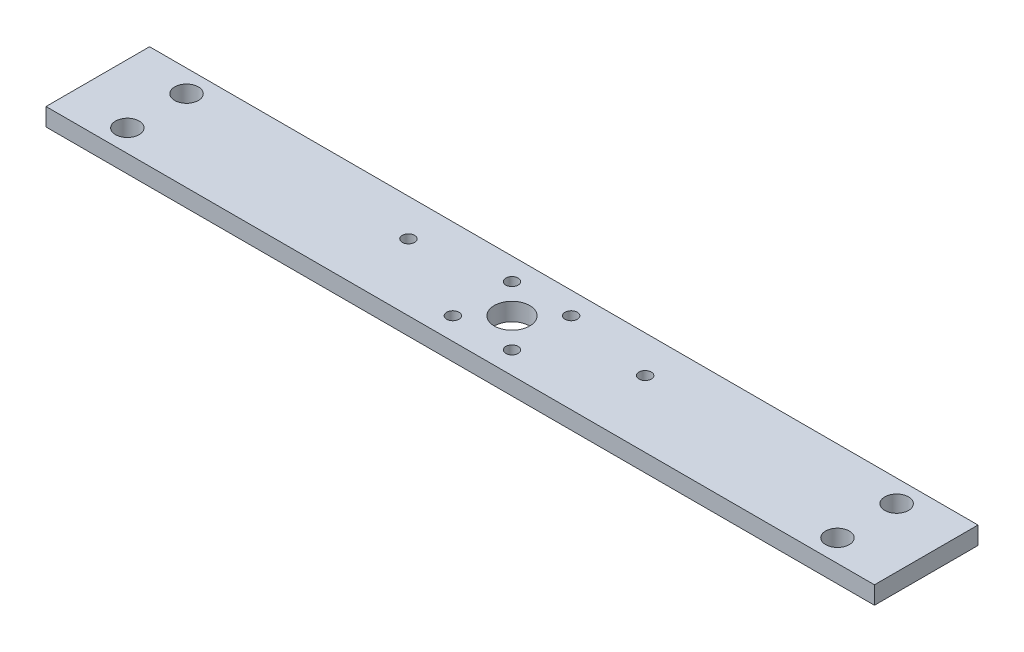
SolidWorks part; units mm, degrees
ref_plane "Front Plane" through (0, 0, 0) normal (0, 0, 1) x (1, 0, 0)
ref_plane "Top Plane" through (0, 0, 0) normal (0, 1, 0) x (1, 0, 0)
ref_plane "Right Plane" through (0, 0, 0) normal (1, 0, 0) x (0, 0, -1)
sketch "Sketch1" plane through (0, 0, 0) normal (0, 1, 0) x (1, 0, 0)
  line L0 (0, -55) -> (0, 55) construction
  line L1 (-140, 17.5) -> (140, 17.5)
  line L2 (-140, 17.5) -> (-140, -17.5)
  line L3 (-140, -17.5) -> (140, -17.5)
  line L4 (140, 17.5) -> (140, -17.5)
  line L5 (-140, 17.5) -> (140, -17.5) construction
  line L6 (-140, -17.5) -> (140, 17.5) construction
  line L7 (10, 10) -> (-10, 10) construction
  line L8 (-55, 0) -> (55, 0) construction
  circle A0 centre (40, 5) radius 2.08
  circle A1 centre (-40, 5) radius 2.08
  circle A2 centre (0, 0) radius 6
  circle A3 centre (10, 10) radius 2.08
  circle A4 centre (-10, 10) radius 2.08
  circle A5 centre (-10, -10) radius 2.08
  circle A6 centre (10, -10) radius 2.08
  circle A7 centre (120, 10) radius 4
  circle A8 centre (-120, 10) radius 4
  circle A9 centre (120, -10) radius 4
  circle A10 centre (-120, -10) radius 4
  point P0 (0, 0)
  point P13 (-40, 5)
  dimension "D3" = 40
  dimension "D5" = 10
  dimension "D10" = 120
  dimension "D1" = 35
  dimension "D2" = 280
  dimension "D4" = 12.5
  dimension "D6" = 10
  dimension "D9" = 20
  dimension "D7" = 2
  dimension "D8" = 2
extrude "Boss-Extrude1" add sketch "Sketch1" along normal blind 6
